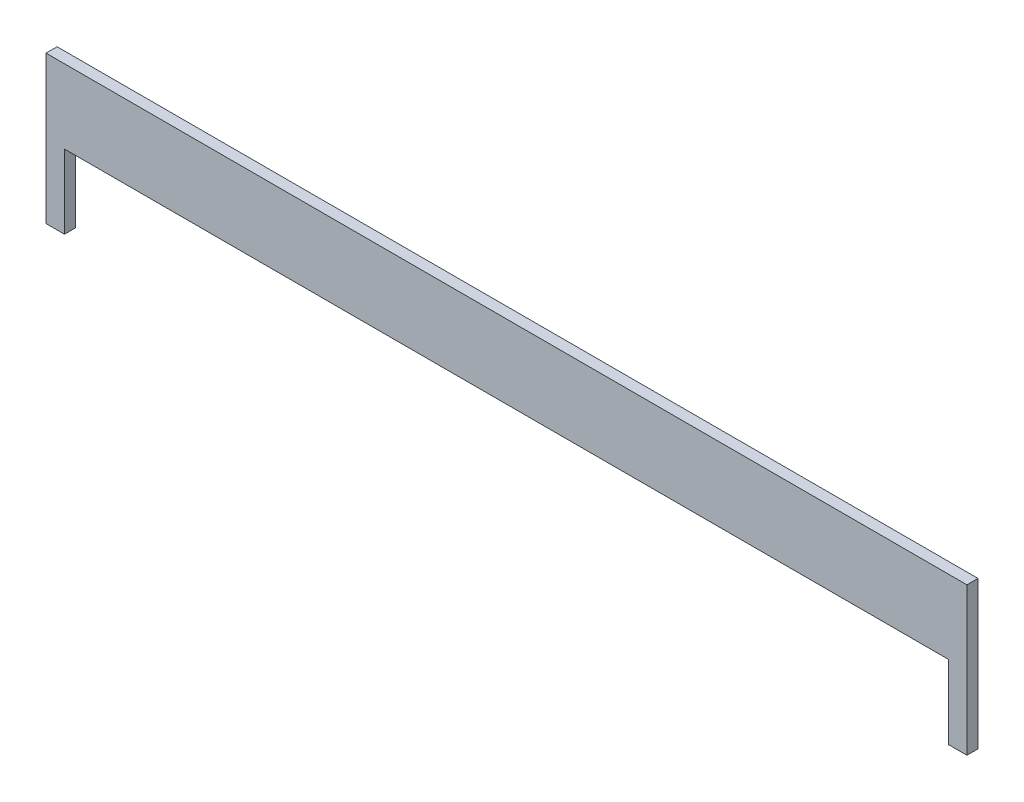
SolidWorks part; units mm, degrees
ref_plane "Front Plane" through (0, 0, 0) normal (0, 0, 1) x (1, 0, 0)
ref_plane "Top Plane" through (0, 0, 0) normal (0, 1, 0) x (1, 0, 0)
ref_plane "Right Plane" through (0, 0, 0) normal (1, 0, 0) x (0, 0, -1)
sketch "Sketch1" plane through (0, 0, 0) normal (0, 0, 1) x (1, 0, 0)
  line L0 (0, 0) -> (249.5, 0)
  line L1 (0, 0) -> (0, -40)
  line L2 (249.5, 0) -> (249.5, -40)
  line L3 (0, -40) -> (249.5, -40)
  dimension "D1" = 40
  dimension "D2" = 249.5
extrude "Boss-Extrude1" add sketch "Sketch1" along normal blind 3
sketch "Sketch2" plane through (0, 0, 3) normal (0, 0, 1) x (1, 0, 0)
  line L0 (5, -40) -> (244.5, -40)
  line L1 (5, -40) -> (5, -20)
  line L2 (244.5, -40) -> (244.5, -20)
  line L3 (5, -20) -> (244.5, -20)
  line L4 (0, 0) -> (0, -40) construction
  line L5 (249.5, -40) -> (249.5, 0) construction
  line L6 (0, -40) -> (249.5, -40) construction
  dimension "D1" = 20
  dimension "D2" = 5
  dimension "D3" = 5
extrude "Cut-Extrude1" cut sketch "Sketch2" against normal blind 5
